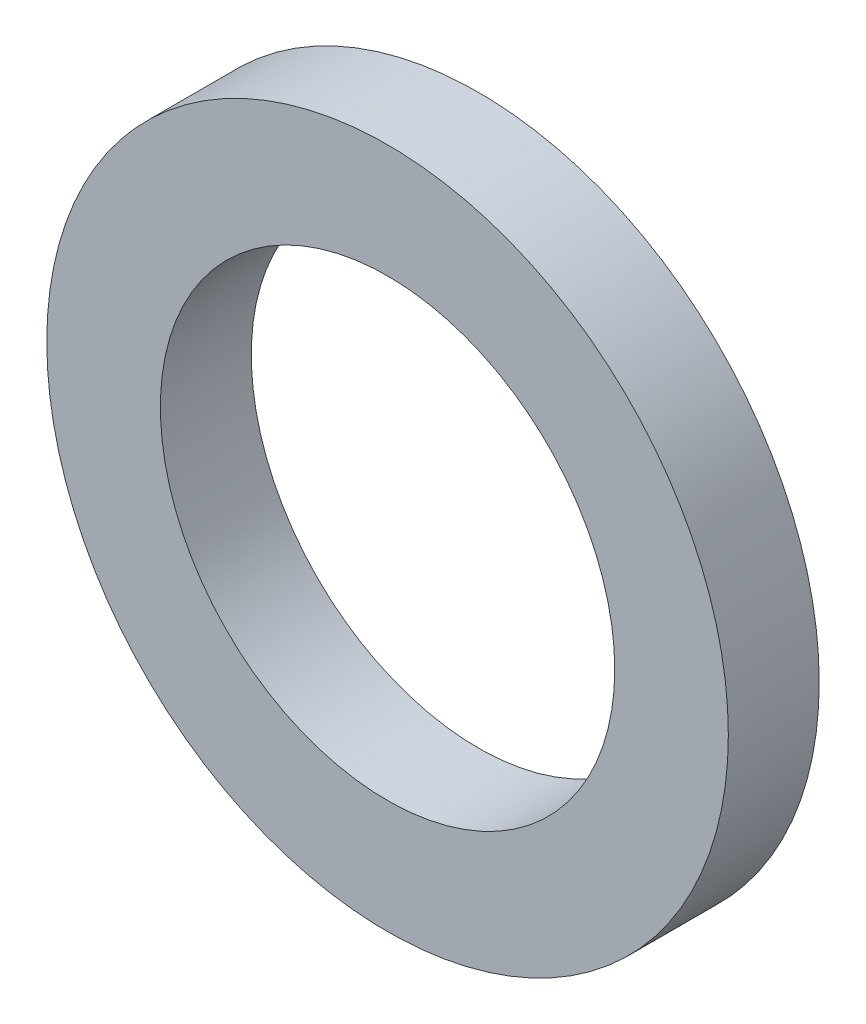
SolidWorks part; units mm, degrees
ref_plane "Front Plane" through (0, 0, 0) normal (0, 0, 1) x (1, 0, 0)
ref_plane "Top Plane" through (0, 0, 0) normal (0, 1, 0) x (1, 0, 0)
ref_plane "Right Plane" through (0, 0, 0) normal (1, 0, 0) x (0, 0, -1)
sketch "Sketch1" plane through (0, 0, 0) normal (0, 0, 1) x (1, 0, 0)
  circle A0 centre (0, 0) radius 6.35
  circle A1 centre (0, 0) radius 9.525
  dimension "D1" = 12.7
  dimension "D2" = 19.05
extrude "Boss-Extrude1" add sketch "Sketch1" along normal blind 2.54
